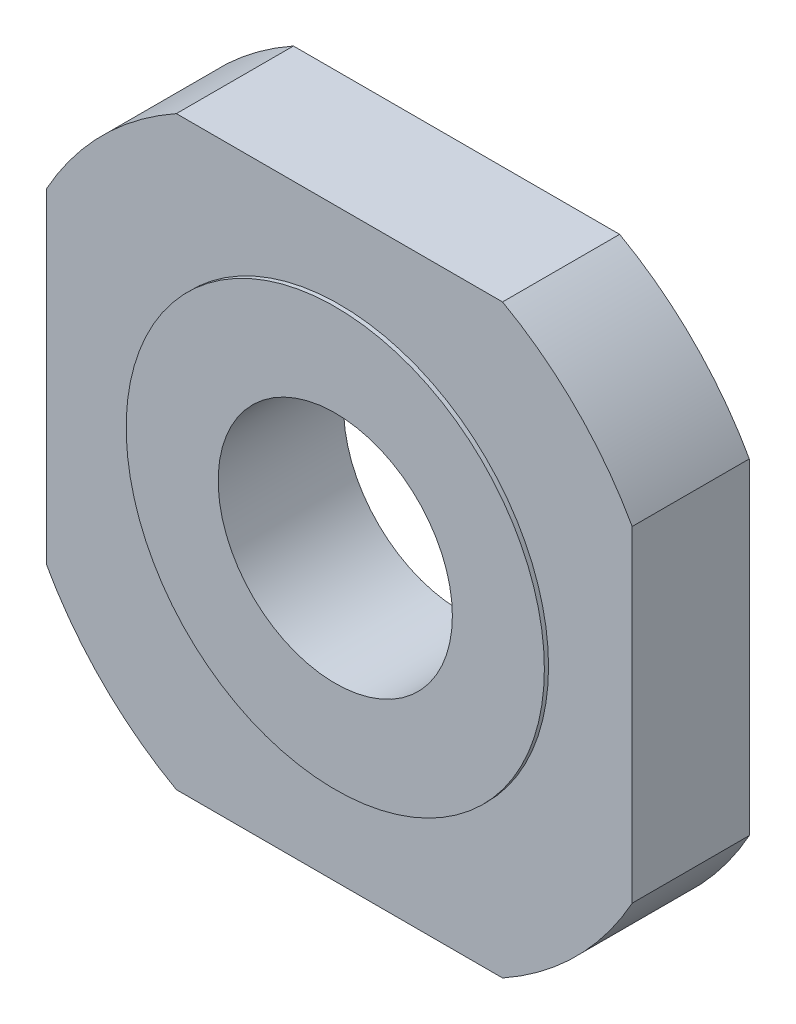
SolidWorks part; units mm, degrees
ref_plane "Front Plane" through (0, 0, 0) normal (0, 0, 1) x (1, 0, 0)
ref_plane "Top Plane" through (0, 0, 0) normal (0, 1, 0) x (1, 0, 0)
ref_plane "Right Plane" through (0, 0, 0) normal (1, 0, 0) x (0, 0, -1)
sketch "Sketch1" plane through (0, 0, 0) normal (0, 0, 1) x (1, 0, 0)
  line L0 (-19.5, 35) -> (19.5, 35)
  line L1 (19.5, 35) -> (35, 19.5) construction
  line L2 (35, 19.5) -> (35, -19.5)
  line L3 (35, -19.5) -> (19.5, -35) construction
  line L4 (19.5, -35) -> (-19.5, -35)
  line L5 (-19.5, -35) -> (-35, -19.5) construction
  line L6 (-35, -19.5) -> (-35, 19.5)
  line L7 (-35, 19.5) -> (-19.5, 35) construction
  line L8 (-19.5, 35) -> (19.5, -35) construction
  arc A0 (-19.5, 35) -> (-35, 19.5) centre (-0.0482, 0.0482) ccw
  arc A1 (19.5, 35) -> (35, 19.5) centre (0.0482, 0.0482) cw
  arc A2 (-35, -19.5) -> (-19.5, -35) centre (-0.0482, -0.0482) ccw
  arc A3 (19.5, -35) -> (35, -19.5) centre (0.0482, -0.0482) ccw
  circle A4 centre (-0.0482, -0.0482) radius 14
  point P8 (0, 0)
  dimension "D4" = 40
  dimension "D5" = 28
  dimension "D1" = 70
  dimension "D2" = 70
  dimension "D3" = 39
extrude "Boss-Extrude1" add sketch "Sketch1" along normal mid plane 14
sketch "Sketch2" plane through (0, 0, 0) normal (0, 0, 1) x (1, 0, 0)
  circle A0 centre (0, 0) radius 25
  circle A1 centre (0, 0) radius 14
  circle A2 centre (-0.0482, -0.0482) radius 14 construction
extrude "Boss-Extrude2" add sketch "Sketch2" along normal mid plane 15
